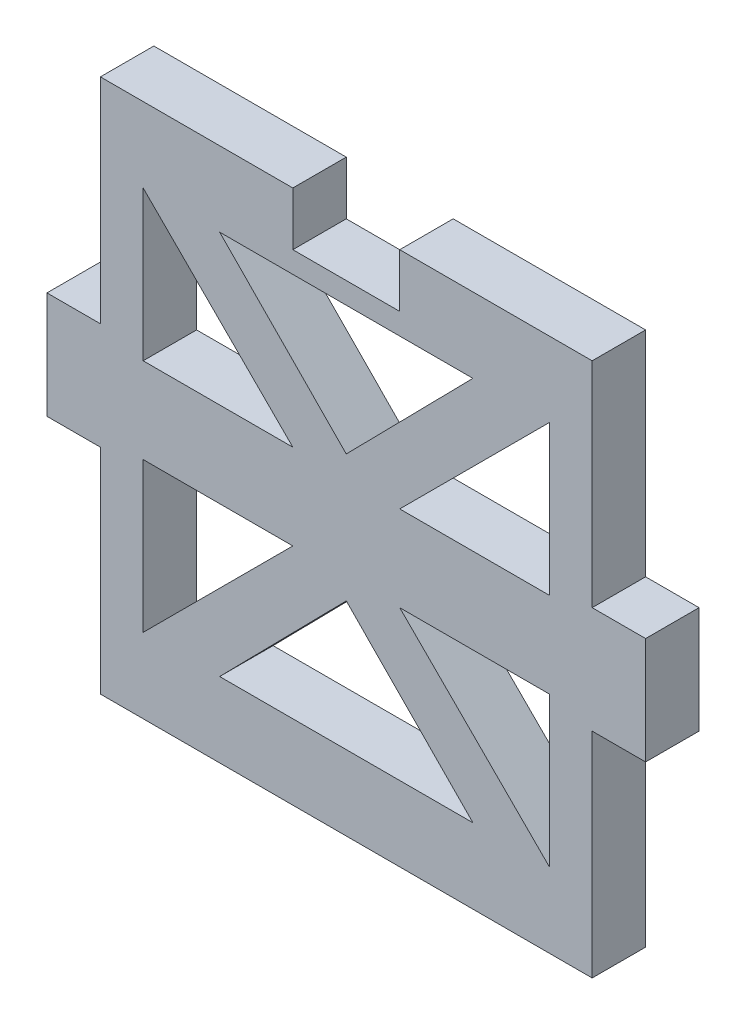
SolidWorks part; units mm, degrees
ref_plane "Front Plane" through (0, 0, 0) normal (0, 0, 1) x (1, 0, 0)
ref_plane "Top Plane" through (0, 0, 0) normal (0, 1, 0) x (1, 0, 0)
ref_plane "Right Plane" through (0, 0, 0) normal (1, 0, 0) x (0, 0, -1)
sketch "Sketch1" plane through (0, 0, 0) normal (0, 0, 1) x (1, 0, 0)
  line L0 (0, -12.7) -> (0, 12.7) construction
  line L1 (-14.605, 15.875) -> (-3.175, 15.875)
  line L2 (-14.605, 15.875) -> (-14.605, 3.175)
  line L3 (0, 0) -> (35.3222, 0) construction
  line L4 (17.78, 3.175) -> (17.78, -3.175)
  line L5 (14.605, 3.175) -> (17.78, 3.175)
  line L6 (3.175, -15.875) -> (-3.175, -15.875)
  line L9 (14.605, 15.875) -> (14.605, 3.175)
  line L10 (14.605, 15.875) -> (3.175, 15.875)
  line L11 (-14.605, 3.175) -> (-17.78, 3.175)
  line L12 (-14.605, -3.175) -> (-17.78, -3.175)
  line L13 (14.605, -15.875) -> (3.175, -15.875)
  line L14 (-17.78, 3.175) -> (-17.78, -3.175)
  line L15 (14.605, -15.875) -> (14.605, -3.175)
  line L19 (14.605, -3.175) -> (17.78, -3.175)
  line L20 (-14.605, -15.875) -> (-14.605, -3.175)
  line L21 (-14.605, -15.875) -> (-3.175, -15.875)
  line L22 (-3.175, 15.875) -> (-3.175, 12.7)
  line L23 (-3.175, 12.7) -> (3.175, 12.7)
  line L24 (3.175, 12.7) -> (3.175, 15.875)
  point P18 (-17.78, 0)
  point P26 (17.78, 0)
  dimension "D1" = 3.175
  dimension "D2" = 35.56
  dimension "D3" = 6.35
  dimension "D4" = 31.75
  dimension "D5" = 3.175
  dimension "D6" = 3.175
extrude "Extrude1" add sketch "Sketch1" along normal blind 3.175
sketch "Sketch2" plane through (0, 0, 3.175) normal (0, 0, 1) x (1, 0, 0)
  line L0 (0, 0) -> (0, 18.705) construction
  line L1 (-23.4299, 0) -> (23.4299, 0) construction
  line L2 (3.175, 2.54) -> (12.065, 11.43)
  line L3 (12.065, 11.43) -> (12.065, 2.54)
  line L4 (12.065, 2.54) -> (3.175, 2.54)
  line L5 (14.605, 3.175) -> (14.605, 15.875) construction
  line L6 (-12.065, 2.54) -> (-3.175, 2.54)
  line L7 (-12.065, 11.43) -> (-12.065, 2.54)
  line L8 (-3.175, 2.54) -> (-12.065, 11.43)
  line L9 (-3.175, -2.54) -> (-12.065, -11.43)
  line L10 (-12.065, -11.43) -> (-12.065, -2.54)
  line L11 (-12.065, -2.54) -> (-3.175, -2.54)
  line L12 (12.065, -2.54) -> (3.175, -2.54)
  line L13 (12.065, -11.43) -> (12.065, -2.54)
  line L14 (3.175, -2.54) -> (12.065, -11.43)
  line L15 (-7.5221, 11.43) -> (7.5221, 11.43)
  line L16 (0, 3.7783) -> (7.5221, 11.43)
  line L17 (0, 3.7783) -> (-7.5221, 11.43)
  line L18 (0, -3.7783) -> (7.5221, -11.43)
  line L19 (0, -3.7783) -> (-7.5221, -11.43)
  line L20 (-7.5221, -11.43) -> (7.5221, -11.43)
  point P23 (0, 11.43)
  dimension "D1" = 8.89
  dimension "D2" = 8.89
  dimension "D3" = 2.54
  dimension "D4" = 2.54
extrude "Cut-Extrude1" cut sketch "Sketch2" against normal up to next
